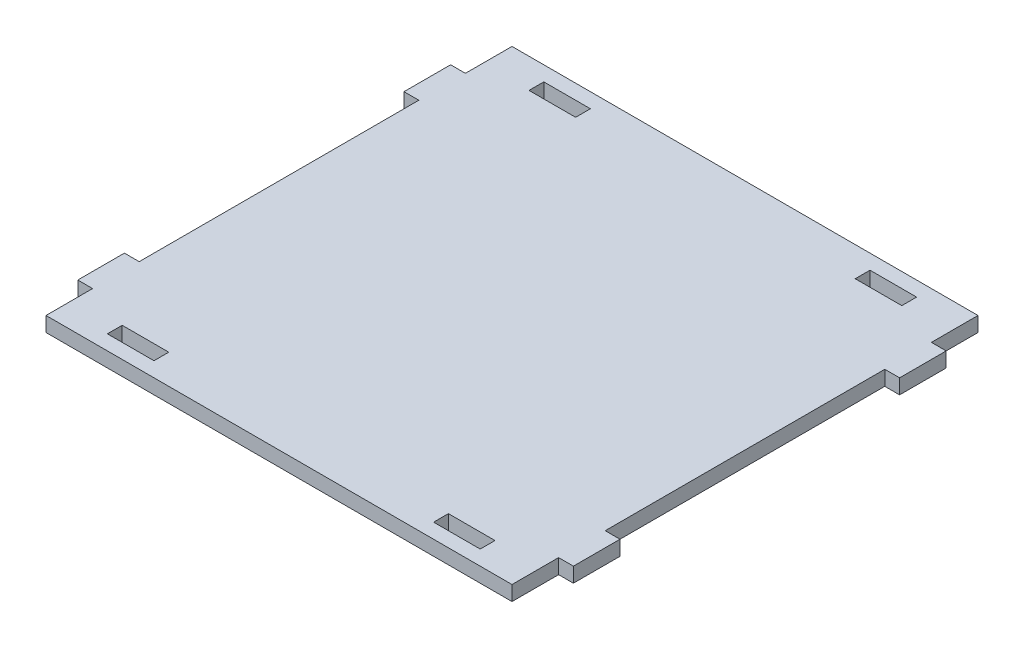
SolidWorks part; units mm, degrees
ref_plane "Front Plane" through (0, 0, 0) normal (0, 0, 1) x (1, 0, 0)
ref_plane "Top Plane" through (0, 0, 0) normal (0, 1, 0) x (1, 0, 0)
ref_plane "Right Plane" through (0, 0, 0) normal (1, 0, 0) x (0, 0, -1)
sketch "Sketch2" plane through (0, 0, 0) normal (0, 1, 0) x (1, 0, 0)
  line L0 (11.4566, -22.9273) -> (135.9041, -22.9273) construction
  line L1 (11.4566, -72.9273) -> (111.4566, -72.9273)
  line L2 (11.4566, -72.9273) -> (11.4566, 27.0727) construction
  line L3 (11.4566, 27.0727) -> (111.4566, 27.0727)
  line L4 (111.4566, -72.9273) -> (111.4566, 27.0727) construction
  line L5 (21.4566, 23.8977) -> (31.4566, 23.8977)
  line L6 (21.4566, 23.8977) -> (21.4566, 20.7227)
  line L7 (21.4566, 20.7227) -> (31.4566, 20.7227)
  line L8 (31.4566, 23.8977) -> (31.4566, 20.7227)
  line L9 (91.4566, 23.8977) -> (101.4566, 23.8977)
  line L10 (91.4566, 23.8977) -> (91.4566, 20.7227)
  line L11 (91.4566, 20.7227) -> (101.4566, 20.7227)
  line L12 (101.4566, 23.8977) -> (101.4566, 20.7227)
  line L13 (101.4566, -69.7523) -> (101.4566, -66.5773)
  line L14 (91.4566, -66.5773) -> (101.4566, -66.5773)
  line L15 (91.4566, -69.7523) -> (91.4566, -66.5773)
  line L16 (91.4566, -69.7523) -> (101.4566, -69.7523)
  line L17 (31.4566, -69.7523) -> (31.4566, -66.5773)
  line L18 (21.4566, -66.5773) -> (31.4566, -66.5773)
  line L19 (21.4566, -69.7523) -> (21.4566, -66.5773)
  line L20 (21.4566, -69.7523) -> (31.4566, -69.7523)
  line L21 (11.4566, 17.0727) -> (11.4566, 27.0727)
  line L22 (11.4566, 17.0727) -> (8.2816, 17.0727)
  line L23 (11.4566, 7.0727) -> (11.4566, -52.9273)
  line L24 (11.4566, 7.0727) -> (8.2816, 7.0727)
  line L25 (8.2816, 17.0727) -> (8.2816, 7.0727)
  line L26 (61.4566, -72.9273) -> (61.4566, 45.6607) construction
  line L27 (11.4566, -62.9273) -> (11.4566, -72.9273)
  line L28 (8.2816, -62.9273) -> (8.2816, -52.9273)
  line L29 (11.4566, -52.9273) -> (8.2816, -52.9273)
  line L30 (11.4566, -62.9273) -> (8.2816, -62.9273)
  line L31 (111.4566, 17.0727) -> (111.4566, 27.0727)
  line L32 (111.4566, -62.9273) -> (114.6316, -62.9273)
  line L33 (111.4566, -52.9273) -> (114.6316, -52.9273)
  line L34 (114.6316, -62.9273) -> (114.6316, -52.9273)
  line L35 (111.4566, -62.9273) -> (111.4566, -72.9273)
  line L36 (114.6316, 17.0727) -> (114.6316, 7.0727)
  line L37 (111.4566, 7.0727) -> (114.6316, 7.0727)
  line L38 (111.4566, 7.0727) -> (111.4566, -52.9273)
  line L39 (111.4566, 17.0727) -> (114.6316, 17.0727)
  dimension "D1" = 100
  dimension "D2" = 100
  dimension "D3" = 10
  dimension "D4" = 10
  dimension "D5" = 3.175
  dimension "D6" = 3.175
  dimension "D7" = 10
  dimension "D8" = 10
  dimension "D9" = 3.175
  dimension "D10" = 3.175
  dimension "D11" = 10
  dimension "D12" = 10
extrude "Boss-Extrude1" add sketch "Sketch2" along normal blind 3.175
